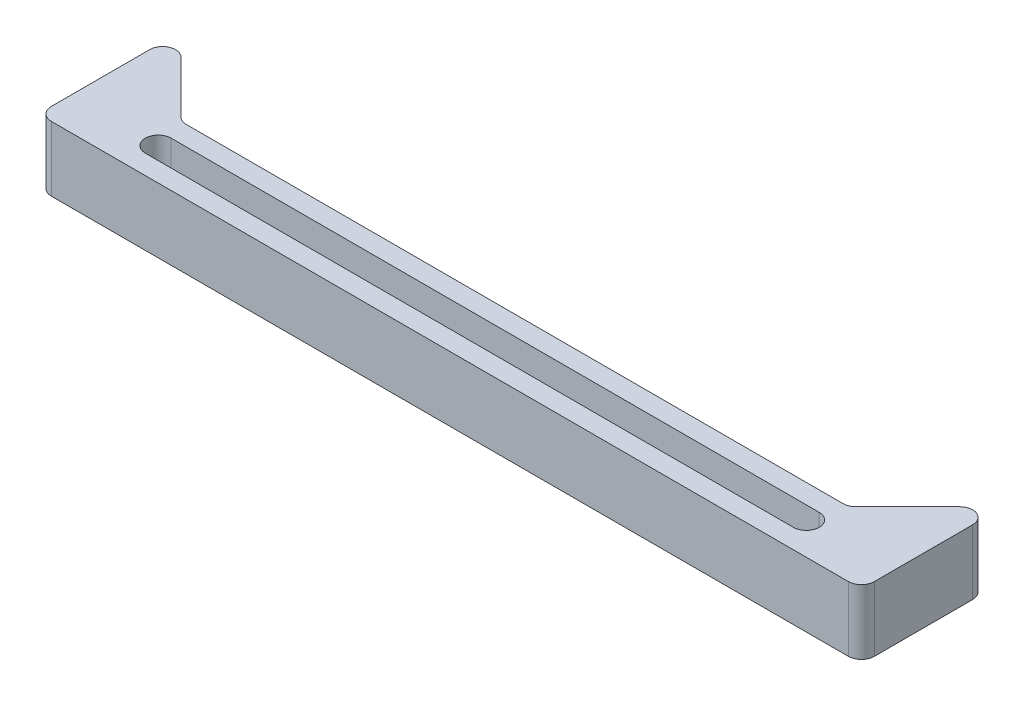
SolidWorks part; units mm, degrees
ref_plane "Front Plane" through (0, 0, 0) normal (0, 0, 1) x (1, 0, 0)
ref_plane "Top Plane" through (0, 0, 0) normal (0, 1, 0) x (1, 0, 0)
ref_plane "Right Plane" through (0, 0, 0) normal (1, 0, 0) x (0, 0, -1)
sketch "Sketch1" plane through (0, 0, 0) normal (0, 1, 0) x (1, 0, 0)
  line L1 (63.5, -5) -> (-63.5, -5)
  line L2 (63.5, -5) -> (63.5, 5)
  line L3 (63.5, 5) -> (-63.5, 5)
  line L4 (-63.5, -5) -> (-63.5, 5)
  line L5 (63.5, -5) -> (-63.5, 5) construction
  line L6 (63.5, 5) -> (-63.5, -5) construction
  point P0 (0, 0)
  dimension "D1" = 10
  dimension "D2" = 127
extrude "Boss-Extrude1" add sketch "Sketch1" along normal blind 10
sketch "Sketch2" plane through (0, 10, 0) normal (0, 1, 0) x (1, 0, 0)
  line L0 (-63.5, 5) -> (-63.5, 17)
  line L1 (-63.5, 17) -> (-51.5, 5)
  line L2 (63.5, 5) -> (-63.5, 5) construction
  line L3 (-51.5, 5) -> (-63.5, 5)
  line L4 (0, 0) -> (0, 17.6814) construction
  line L5 (51.5, 5) -> (63.5, 5)
  line L6 (63.5, 17) -> (51.5, 5)
  line L7 (63.5, 5) -> (63.5, 17)
  dimension "D1" = 12
  dimension "D2" = 12
extrude "Boss-Extrude2" add sketch "Sketch2" against normal up to surface (10 mm away) up to face at (0, 0, 0)
fillet "Fillet1" radius 2 6 edges at (63.5, 5, -17) (51.5, 5, -5) (-51.5, 5, -5) (-63.5, 5, -17) (63.5, 5, 5) (-63.5, 5, 5)
sketch "Sketch4" plane through (0, 10, 0) normal (0, 1, 0) x (1, 0, 0)
  line L0 (-50, 0) -> (50, 0) construction
  line L1 (-50, 2) -> (50, 2)
  line L2 (-50, -2) -> (50, -2)
  arc A0 (-50, 2) -> (-50, -2) centre (-50, 0) ccw
  arc A1 (50, -2) -> (50, 2) centre (50, 0) ccw
  point P2 (0, 0)
  point P7 (0, 0)
  dimension "D2" = 2
  dimension "D1" = 100
extrude "Cut-Extrude1" cut sketch "Sketch4" against normal up to next
